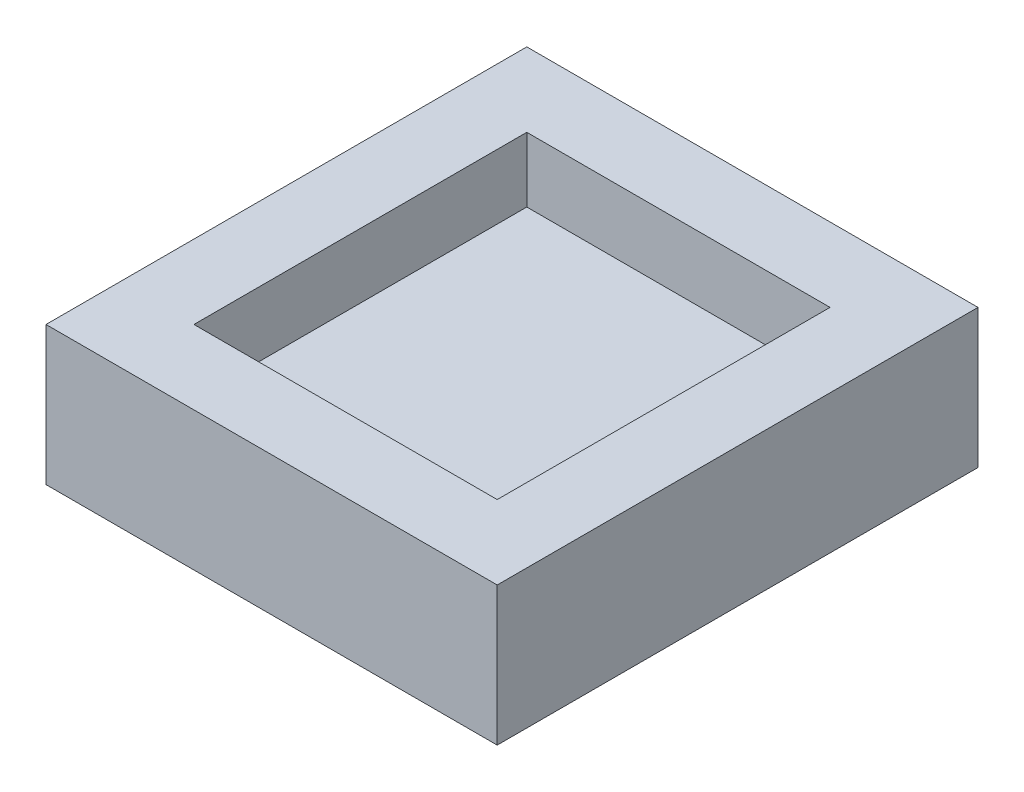
SolidWorks part; units mm, degrees
ref_plane "Front Plane" through (0, 0, 0) normal (0, 0, 1) x (1, 0, 0)
ref_plane "Top Plane" through (0, 0, 0) normal (0, 1, 0) x (1, 0, 0)
ref_plane "Right Plane" through (0, 0, 0) normal (1, 0, 0) x (0, 0, -1)
sketch "Sketch1" plane through (0, 0, 0) normal (0, 1, 0) x (1, 0, 0)
  line L1 (-30.5, -32.5) -> (30.5, -32.5)
  line L2 (-30.5, -32.5) -> (-30.5, 32.5)
  line L3 (-30.5, 32.5) -> (30.5, 32.5)
  line L4 (30.5, -32.5) -> (30.5, 32.5)
  line L5 (-30.5, -32.5) -> (30.5, 32.5) construction
  line L6 (-30.5, 32.5) -> (30.5, -32.5) construction
  point P0 (0, 0)
  dimension "D1" = 65
  dimension "D2" = 61
extrude "Boss-Extrude1" add sketch "Sketch1" along normal blind 18.75
sketch "Sketch2" plane through (0, 18.75, 0) normal (0, 1, 0) x (1, 0, 0)
  line L1 (-20.5, 22.5) -> (20.5, 22.5)
  line L2 (-20.5, 22.5) -> (-20.5, -22.5)
  line L3 (-20.5, -22.5) -> (20.5, -22.5)
  line L4 (20.5, 22.5) -> (20.5, -22.5)
  line L5 (-20.5, 22.5) -> (20.5, -22.5) construction
  line L6 (-20.5, -22.5) -> (20.5, 22.5) construction
  point P0 (0, 0)
  dimension "D1" = 45
  dimension "D2" = 41
extrude "Cut-Extrude1" cut sketch "Sketch2" against normal blind 8.75
